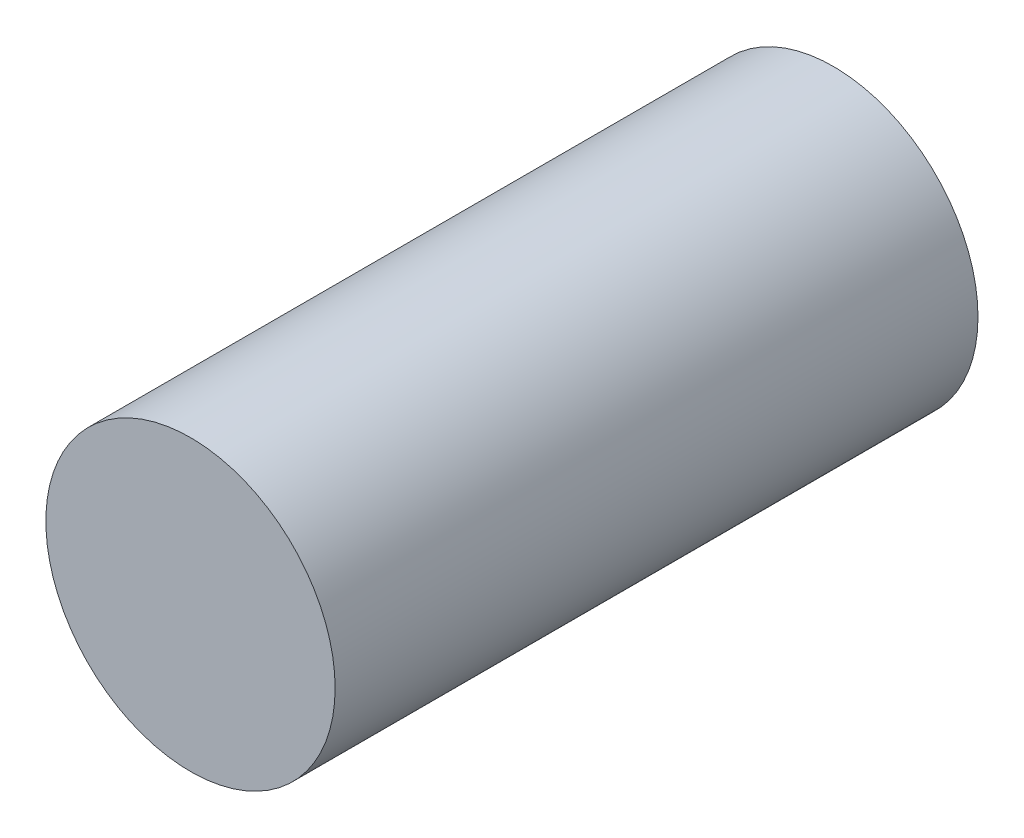
SolidWorks part; units mm, degrees
ref_plane "Front Plane" through (0, 0, 0) normal (0, 0, 1) x (1, 0, 0)
ref_plane "Top Plane" through (0, 0, 0) normal (0, 1, 0) x (1, 0, 0)
ref_plane "Right Plane" through (0, 0, 0) normal (1, 0, 0) x (0, 0, -1)
sketch "Sketch1" plane through (0, 0, 0) normal (0, 0, 1) x (1, 0, 0)
  circle A0 centre (0, 0) radius 4.5
extrude "Boss-Extrude1" add sketch "Sketch1" along normal blind 20
sketch "Sketch2" plane through (0, 0, 0) normal (0, 0, 1) x (1, 0, 0)
  circle A0 centre (0, 0) radius 1
extrude "Cut-Extrude1" cut sketch "Sketch2" along normal blind 15
